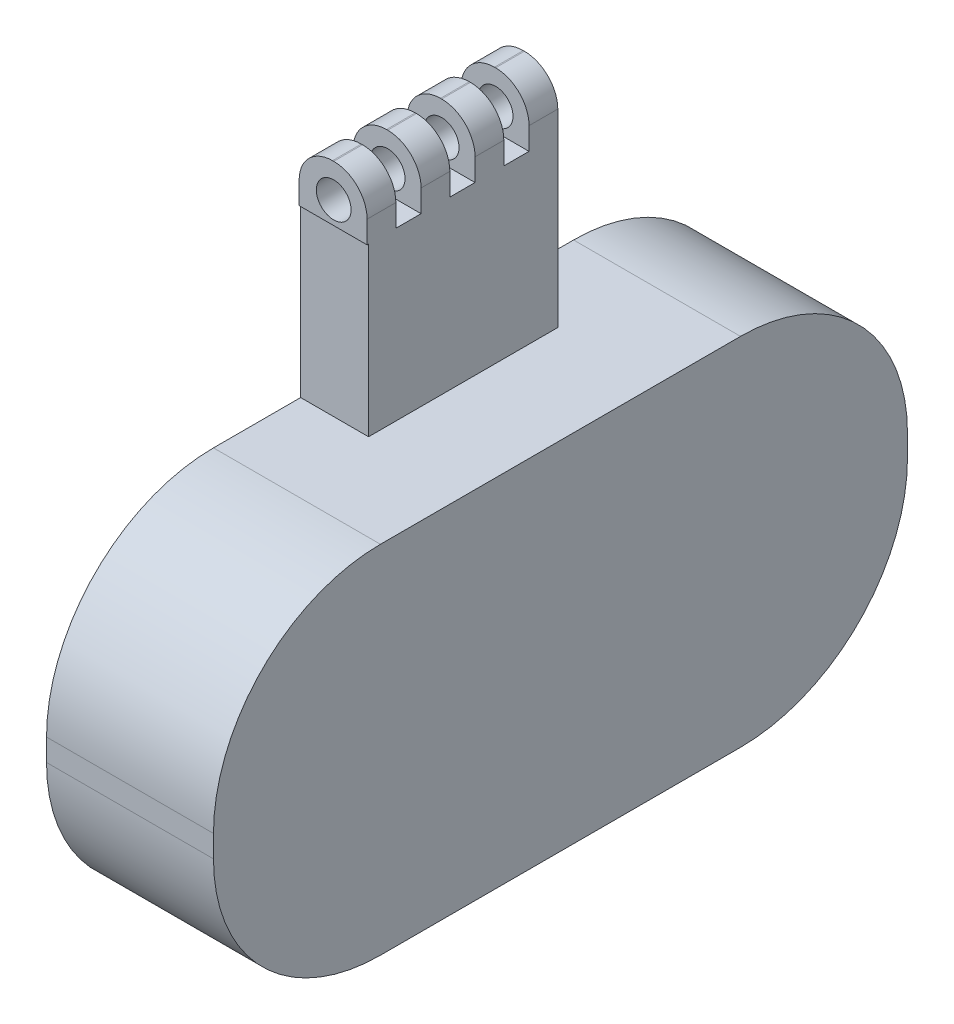
SolidWorks part; units mm, degrees
ref_plane "Front Plane" through (0, 0, 0) normal (0, 0, 1) x (1, 0, 0)
ref_plane "Top Plane" through (0, 0, 0) normal (0, 1, 0) x (1, 0, 0)
ref_plane "Right Plane" through (0, 0, 0) normal (1, 0, 0) x (0, 0, -1)
sketch "Sketch1" plane through (0, 0, 0) normal (1, 0, 0) x (0, 0, -1)
  line L1 (-32.3513, 31.9783) -> (32.3513, 31.9783)
  line L2 (-62.3513, 1.9783) -> (-62.3513, -1.9783)
  line L3 (-32.3513, -31.9783) -> (32.3513, -31.9783)
  line L4 (62.3513, 1.9783) -> (62.3513, -1.9783)
  line L5 (-62.3513, 31.9783) -> (62.3513, -31.9783) construction
  line L6 (-62.3513, -31.9783) -> (62.3513, 31.9783) construction
  arc A0 (-62.3513, -1.9783) -> (-32.3513, -31.9783) centre (-32.3513, -1.9783) ccw
  arc A1 (32.3513, -31.9783) -> (62.3513, -1.9783) centre (32.3513, -1.9783) ccw
  arc A2 (32.3513, 31.9783) -> (62.3513, 1.9783) centre (32.3513, 1.9783) cw
  arc A3 (-32.3513, 31.9783) -> (-62.3513, 1.9783) centre (-32.3513, 1.9783) ccw
  point P0 (0, 0)
  dimension "D1" = 30
extrude "Boss-Extrude1" add sketch "Sketch1" along normal blind 30
sketch "Sketch4" plane through (0, 31.9783, 0) normal (0, 1, 0) x (1, 0, 0)
  line L0 (0, 32.3513) -> (0, -32.3513) construction
  line L1 (0, -16.6918) -> (12.2105, -16.6918)
  line L2 (0, -16.6918) -> (0, 17.3082)
  line L3 (0, 17.3082) -> (12.2105, 17.3082)
  line L4 (12.2105, -16.6918) -> (12.2105, 17.3082)
  line L5 (6.1053, 17.3082) -> (6.1053, -16.6918) construction
  line L6 (0, 0.3082) -> (12.2105, 0.3082) construction
  point P384 (6.1053, 0.3082)
  dimension "D1" = 34
extrude "Boss-Extrude3" add sketch "Sketch4" along normal blind 30
sketch "Sketch5" plane through (0, 61.9783, 0) normal (0, 1, 0) x (1, 0, 0)
  line L0 (12.2105, -16.6918) -> (12.2105, 17.3082) construction
  line L1 (0, 17.3082) -> (12.2105, 17.3082)
  line L2 (0, 17.3082) -> (0, 12.1401)
  line L3 (0, 12.1401) -> (12.2105, 12.1401)
  line L4 (12.2105, 17.3082) -> (12.2105, 12.1401)
  line L5 (6.1053, 12.1401) -> (6.1053, 17.3082) construction
  line L6 (0, 14.7241) -> (12.2105, 14.7241) construction
  point P184 (6.1053, 14.7241)
extrude "Boss-Extrude4" add sketch "Sketch5" along normal blind 10
fillet "Fillet1" radius 6 2 edges at (12.2105, 71.9783, -14.7241) (0, 71.9783, -14.7241)
pattern_linear "LPattern1" count 4 spacing 9.7 along (0, 0, 1) of "Boss-Extrude4", "Fillet1"
sketch "Sketch6" plane through (0, 0, 16.9599) normal (0, 0, 1) x (1, 0, 0)
  circle A0 centre (6.2105, 65.9783) radius 3.1214
  arc A1 (12.2105, 65.9783) -> (6.2105, 71.9783) centre (6.2105, 65.9783) ccw construction
  dimension "D1" = 0
extrude "Cut-Extrude1" cut sketch "Sketch6" against normal through all
sketch "Sketch10" plane through (0, -31.9783, 0) normal (0, -1, 0) x (1, 0, 0)
  line L1 (2.6723, -19.6613) -> (8.4312, -19.6613)
  line L2 (2.6723, -19.6613) -> (2.6723, 19.3013)
  line L3 (2.6723, 19.3013) -> (8.4312, 19.3013)
  line L4 (8.4312, -19.6613) -> (8.4312, 19.3013)
  line L5 (5.5518, 19.3013) -> (5.5518, -19.6613) construction
  line L6 (2.6723, -0.18) -> (8.4312, -0.18) construction
  point P344 (5.5518, -0.18)
extrude "Cut-Extrude2" cut sketch "Sketch10" against normal blind 35
sketch "Sketch11" plane through (0, 3.0217, 0) normal (0, -1, 0) x (1, 0, 0)
  line L1 (3.6693, -7.739) -> (7.5687, -7.739)
  line L2 (3.6693, -7.739) -> (3.6693, 8.535)
  line L3 (3.6693, 8.535) -> (7.5687, 8.535)
  line L4 (7.5687, -7.739) -> (7.5687, 8.535)
  line L5 (5.619, 8.535) -> (5.619, -7.739) construction
  line L6 (3.6693, 0.398) -> (7.5687, 0.398) construction
  point P296 (5.619, 0.398)
extrude "Boss-Extrude5" add sketch "Sketch11" along normal blind 50
